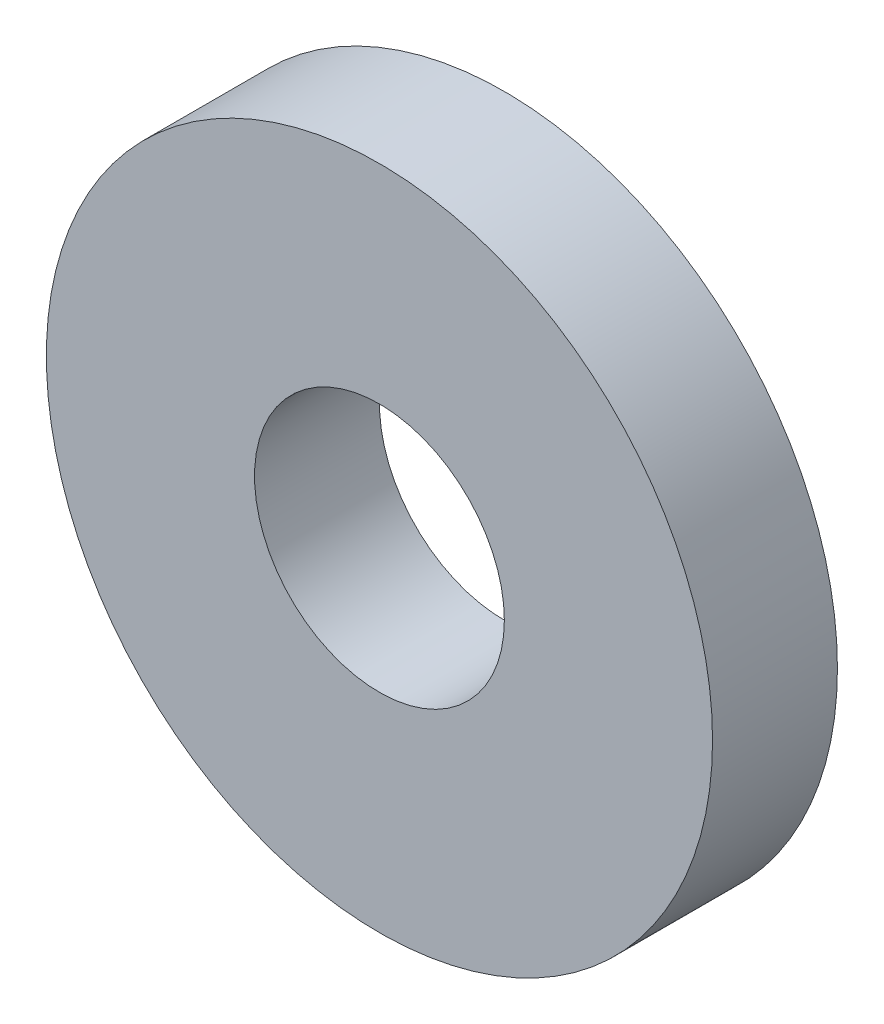
SolidWorks part; units mm, degrees
ref_plane "Front Plane" through (0, 0, 0) normal (0, 0, 1) x (1, 0, 0)
ref_plane "Top Plane" through (0, 0, 0) normal (0, 1, 0) x (1, 0, 0)
ref_plane "Right Plane" through (0, 0, 0) normal (1, 0, 0) x (0, 0, -1)
sketch "Sketch1" plane through (0, 0, 0) normal (0, 0, 1) x (1, 0, 0)
  circle A0 centre (0, 0) radius 40
  circle A1 centre (0, 0) radius 15
extrude "Boss-Extrude1" add sketch "Sketch1" along normal blind 15
